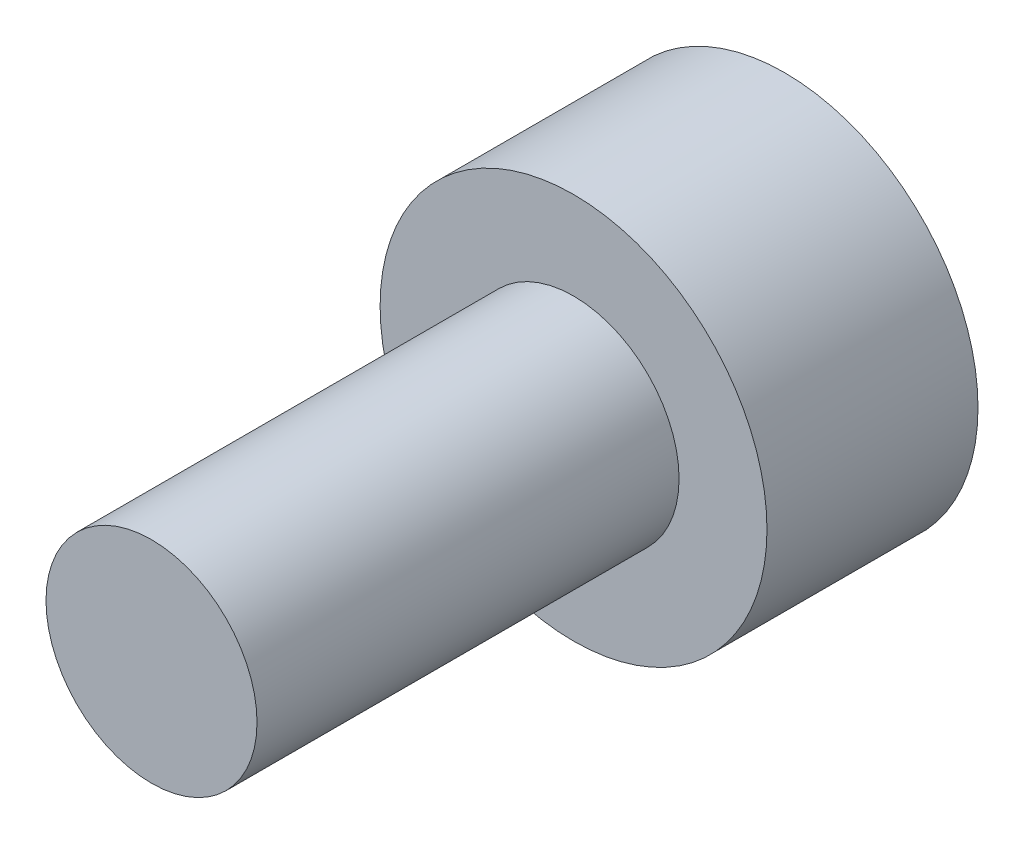
SolidWorks part; units mm, degrees
ref_plane "Plano frontal" through (0, 0, 0) normal (0, 0, 1) x (1, 0, 0)
ref_plane "Plano superior" through (0, 0, 0) normal (0, 1, 0) x (1, 0, 0)
ref_plane "Plano direito" through (0, 0, 0) normal (1, 0, 0) x (0, 0, -1)
sketch "Esboço1" plane through (0, 0, 0) normal (0, 1, 0) x (1, 0, 0)
  line L0 (0, 0) -> (2.75, 0)
  line L1 (2.75, 0) -> (2.75, -3)
  line L2 (2.75, -3) -> (1.5, -3)
  line L3 (0, -3) -> (0, 0)
  line L5 (1.5, -3) -> (1.5, -9)
  line L6 (1.5, -9) -> (0, -9)
  line L7 (0, -9) -> (0, -3)
revolve "Revolução1" add sketch "Esboço1" angle 360 about L3
sketch "Esboço2" plane through (0, 0, 0) normal (0, 0, -1) x (-1, 0, 0)
  line L1 (1.7321, 0) -> (0.866, 1.5)
  line L2 (0.866, 1.5) -> (-0.866, 1.5)
  line L3 (-0.866, 1.5) -> (-1.7321, 0)
  line L4 (-1.7321, 0) -> (-0.866, -1.5)
  line L5 (-0.866, -1.5) -> (0.866, -1.5)
  line L6 (0.866, -1.5) -> (1.7321, 0)
  circle A0 centre (0, 0) radius 1.5 construction
extrude "Corte-extrusão1" cut sketch "Esboço2" against normal blind 1.5
